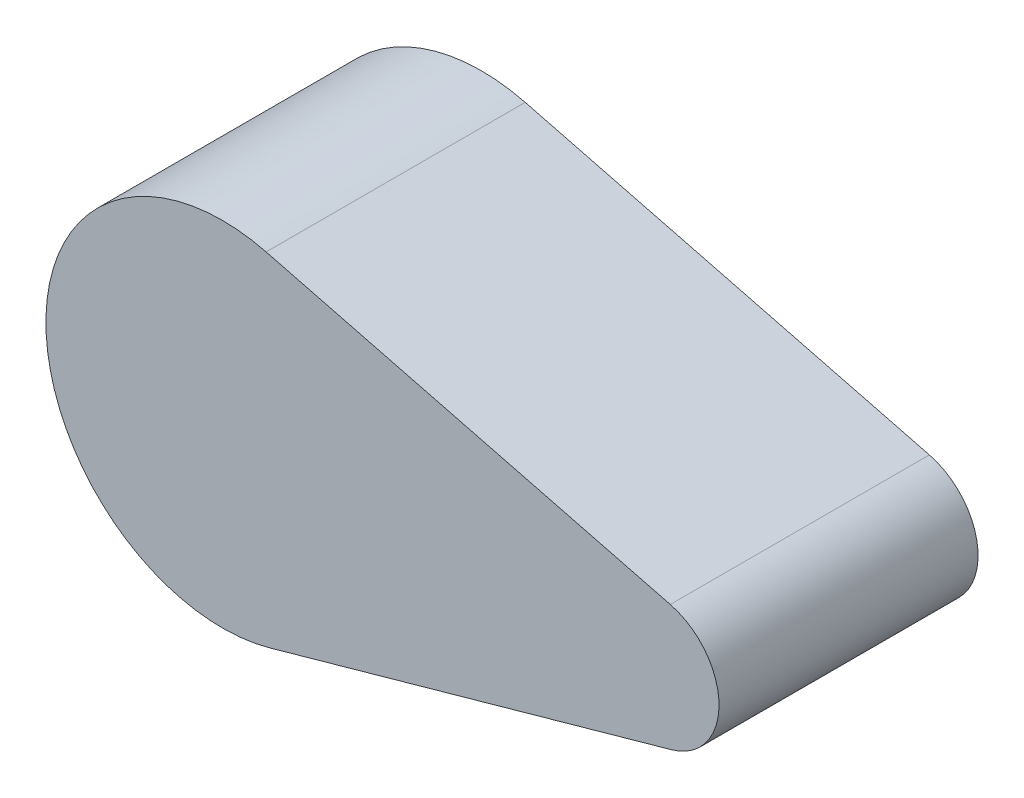
SolidWorks part; units mm, degrees
ref_plane "Front Plane" through (0, 0, 0) normal (0, 0, 1) x (1, 0, 0)
ref_plane "Top Plane" through (0, 0, 0) normal (0, 1, 0) x (1, 0, 0)
ref_plane "Right Plane" through (0, 0, 0) normal (1, 0, 0) x (0, 0, -1)
sketch "Sketch1" plane through (0, 0, 0) normal (0, 0, 1) x (1, 0, 0)
  line L0 (28.0454, -99.9857) -> (264.2897, -33.7204)
  line L1 (25.7048, 100.6129) -> (263.4309, 39.8781)
  arc A0 (264.2897, -33.7204) -> (263.4309, 39.8781) centre (254, 2.9638) ccw
  arc A1 (28.0454, -99.9857) -> (25.7048, 100.6129) centre (0, 0) cw
  dimension "D1" = 38.1
  dimension "D2" = 30
  dimension "D3" = 254
extrude "Boss-Extrude1" add sketch "Sketch1" against normal blind 152.4
